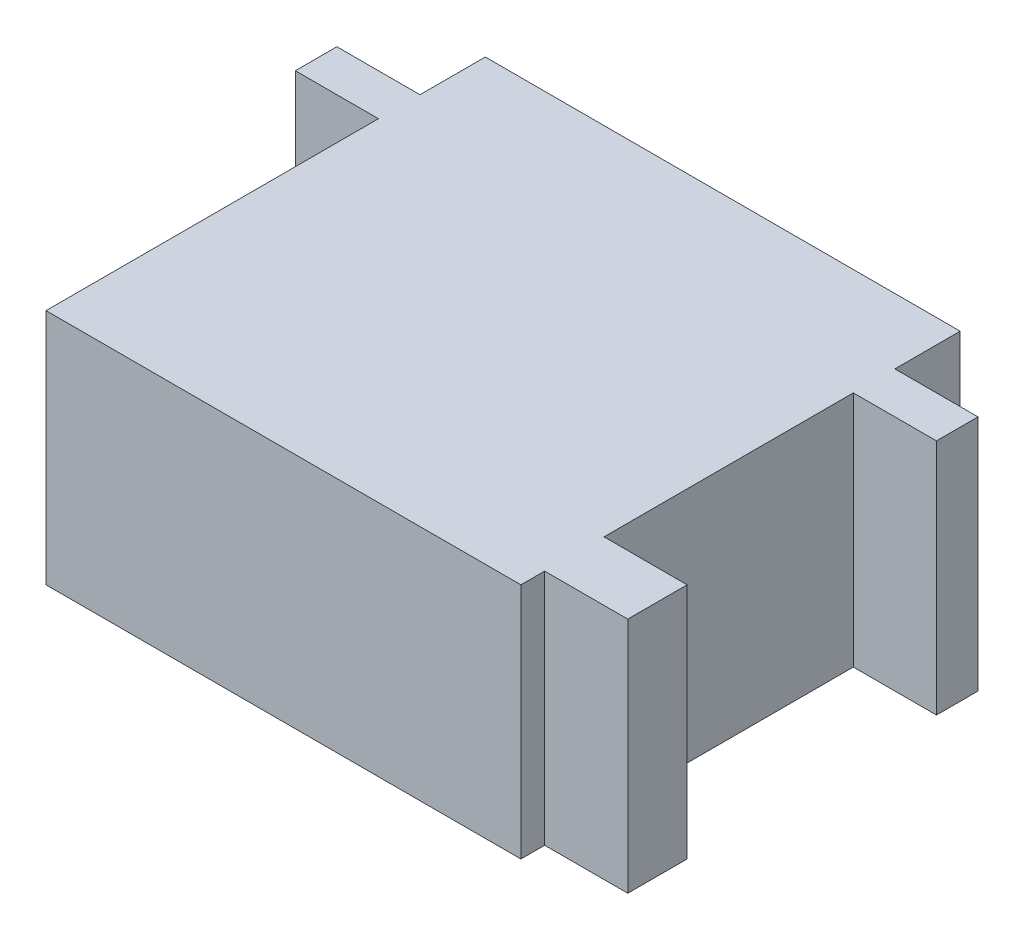
SolidWorks part; units mm, degrees
ref_plane "Plan de face" through (0, 0, 0) normal (0, 0, 1) x (1, 0, 0)
ref_plane "Plan de dessus" through (0, 0, 0) normal (0, 1, 0) x (1, 0, 0)
ref_plane "Plan de droite" through (0, 0, 0) normal (1, 0, 0) x (0, 0, -1)
sketch "Esquisse1" plane through (0, 0, 0) normal (0, 1, 0) x (1, 0, 0)
  line L0 (20, 0) -> (20, 37) construction
  line L1 (0, 0) -> (40, 0)
  line L2 (0, 0) -> (0, 28)
  line L3 (0, 37) -> (40, 37)
  line L4 (40, 0) -> (40, 2)
  line L5 (40, 31.5) -> (47, 31.5)
  line L7 (40, 28) -> (47, 28)
  line L8 (47, 31.5) -> (47, 28)
  line L9 (40, 7) -> (47, 7)
  line L11 (40, 2) -> (47, 2)
  line L12 (47, 7) -> (47, 2)
  line L13 (33, 37) -> (27, 37)
  line L17 (40, 31.5) -> (40, 37)
  line L18 (0, 28) -> (-7, 28)
  line L19 (-7, 31.5) -> (-7, 28)
  line L20 (0, 31.5) -> (-7, 31.5)
  line L21 (0, 31.5) -> (0, 37)
  line L22 (40, 7) -> (40, 28)
  dimension "D1" = 40
  dimension "D4" = 7
  dimension "D5" = 5
  dimension "D6" = 2
  dimension "D7" = 37
  dimension "D8" = 28
  dimension "D9" = 3.5
  dimension "D10" = 7
extrude "Boss.-Extru.1" add sketch "Esquisse1" along normal blind 20 contours L1 L0 L3 L21 L20 L19 L18 L2 | L0 L1 L4 L11 L12 L9 L22 L7 L8 L5 L17 L3
sketch "Esquisse2" plane through (0, 0, -37) normal (0, 0, -1) x (-1, 0, 0)
  line L0 (-40, 10) -> (-30, 10) construction
  line L1 (-40, 20) -> (-40, 0) construction
  circle A0 centre (-30, 10) radius 3
  dimension "D2" = 6
  dimension "D1" = 10
extrude "Boss.-Extru.2" add sketch "Esquisse2" along normal blind 5
sketch "Esquisse3" plane through (0, 0, -42) normal (0, 0, -1) x (-1, 0, 0)
  circle A0 centre (-30, 10) radius 20
  dimension "D1" = 40
